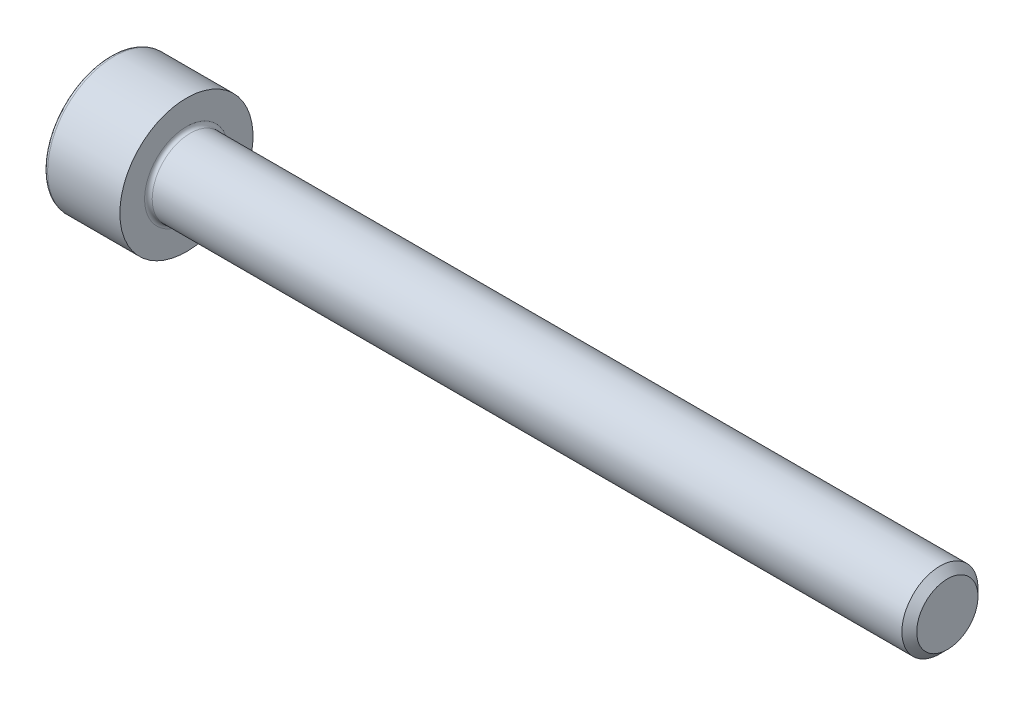
SolidWorks part; units mm, degrees
revolve "Base-Revolve" add sketch "BodySke"
sketch "BodySke" plane through (0, 0, 0) normal (0, 0, 1) x (1, 0, 0)
  line L0 (0, 0) -> (0, 3.5)
  line L1 (0, 3.5) -> (4, 3.5)
  line L2 (4, 3.5) -> (4, 2)
  line L3 (4, 2) -> (43.61, 2)
  line L4 (44, 1.61) -> (44, 0)
  line L5 (44, 0) -> (0, 0)
  line L6 (-31.75, 0) -> (127, 0) construction
  line L8 (44, 1.61) -> (43.61, 2)
  line L10 (44, -1.61) -> (43.61, -2) construction
  line L11 (4.7, 9.525) -> (4.7, 3.175) construction
  line L12 (24, 9.525) -> (24, 3.175) construction
  line L13 (-16, 9.525) -> (-16, 3.175) construction
  dimension "Body_ch_ang" = 45
  dimension "Thread_length" = 60
cosmetic thread "ThreadCosmetic" [suppressed]
fillet "Fillet1" radius 0.2 1 edges at (4, 0, 2)
fillet "Fillet2" radius 0.2 1 edges at (0, 0, 3.5)
ref_plane "Plane1" through (0, 0, 0) normal (0, 0, 1) x (1, 0, 0)
ref_plane "Plane2" through (0, 0, 0) normal (0, 1, 0) x (1, 0, 0)
ref_plane "Plane3" through (0, 0, 0) normal (1, 0, 0) x (0, 0, -1)
sketch "Sketch2" plane through (0, 0, 0) normal (0, 0, 1) x (1, 0, 0)
  line L0 (0, 1.5355) -> (2, 1.5355)
  line L1 (2, 1.5355) -> (2.8865, 0)
  line L2 (-31.75, 0) -> (127, 0) construction
  line L3 (2.8865, 0) -> (0, 0)
  line L4 (0, 0) -> (0, 1.5355)
  line L6 (0, 0) -> (47.625, 0) construction
  dimension "D2" = 60
revolve "Hex-PreBroach" cut sketch "Sketch2" angle 360 about L6
sketch "Sketch3" plane through (0, 0, 0) normal (-1, 0, 0) x (0, 0.5, 0.866)
  line L0 (0.8865, 1.5355) -> (-0.8865, 1.5355)
  line L1 (-0.8865, 1.5355) -> (-1.773, 0)
  line L2 (0.8865, 1.5355) -> (1.773, 0)
  line L3 (0.8865, -1.5355) -> (1.773, 0)
  line L4 (0.8865, -1.5355) -> (-0.8865, -1.5355)
  line L5 (-0.8865, -1.5355) -> (-1.773, 0)
extrude "Hex" cut sketch "Sketch3" against normal blind 2
sketch "ThdSchSke" plane through (0, 0, 0) normal (0, 0, 1) x (1, 0, 0)
  line L0 (24, -1.61) -> (23.7269, -2)
  line L1 (24, -1.61) -> (24.2731, -2)
  line L2 (24.2731, -2) -> (24.2731, -2.5)
  line L3 (-3.175, 0) -> (5.1513, 0) construction
  line L4 (0, 3.3) -> (0, -3.3) construction
  line L5 (24.2731, -2.5) -> (23.7269, -2.5)
  line L6 (23.7269, -2.5) -> (23.7269, -2)
revolve "ThreadSchematic" [suppressed] cut sketch "ThdSchSke" angle 360 about L3
pattern_linear "ThdSchPat" [suppressed]
equation "\"D2@Sketch3\" = \"Hex_size@Sketch3\" / 2"
equation "\"D1@Sketch3\" = \"Hex_size@Sketch3\" / 2"
equation "\"D1@Sketch2\" = \"Hex_size@Sketch3\" / 2"
equation "\"Thread_minor@ThreadCosmetic\"  =  \"Minor_dia@BodySke\""
equation "\"Depth@Sketch2\" =  \"Key_eng@Hex\""
equation "\"Thread_length@ThreadCosmetic\" = ((sgn( (\"Length@BodySke\" - \"Advance@BodySke\" * 3.0) - \"Thread_nom@BodySke\" )-1)*( (\"Length@BodySke\" - \"Advance@BodySke\" * 3.0) - \"Thread_nom@BodySke\" ))/-2+ \"Thread_nom@BodySke\""
equation "\"Thread_minor@ThdSchSke\" = \"Minor_dia@BodySke\""
equation "\"Diameter@ThdSchSke\" = \"Diameter@BodySke\""
equation "\"Overcut@ThdSchSke\" = \"Diameter@BodySke\" * 1.25"
equation "\"Start@ThdSchSke\" = \"Head_ht@BodySke\" + \"Length@BodySke\" - \"Thread_length@ThreadCosmetic\"  '---Non-countersunk---"
equation "\"Num_threads@ThdSchPat\" = int( \"Thread_length@ThreadCosmetic\" / \"Advance@BodySke\" + 0.999 )  + 1"
equation "\"Advance@ThdSchPat\" = \"Thread_length@ThreadCosmetic\" /  (\"Num_threads@ThdSchPat\" - 1) 'relax it"
equation "\"Num_threads@ThdSchPat\" = \"Num_threads@ThdSchPat\" - sgn( \"Num_threads@ThdSchPat\" - 1) '---chamfered tips only---"
